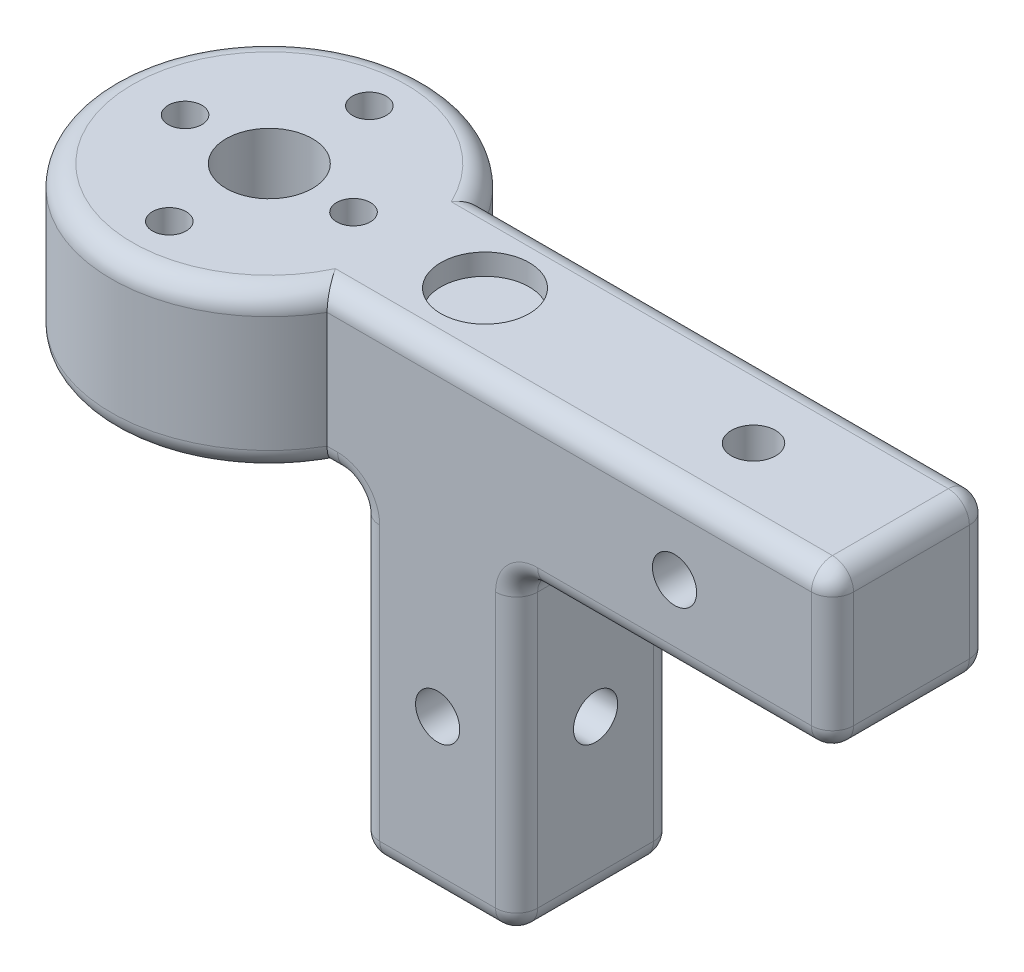
SolidWorks part; units mm, degrees
ref_plane "Front Plane" through (0, 0, 0) normal (0, 0, 1) x (1, 0, 0)
ref_plane "Top Plane" through (0, 0, 0) normal (0, 1, 0) x (1, 0, 0)
ref_plane "Right Plane" through (0, 0, 0) normal (1, 0, 0) x (0, 0, -1)
sketch "Sketch1" plane through (0, 0, 0) normal (0, 1, 0) x (1, 0, 0)
  line L0 (0, 0) -> (60.9904, 0) construction
  line L1 (12.9904, 7.5) -> (60.9904, 7.5)
  line L2 (15.9904, 7.5) -> (15.9904, -7.5) construction
  line L3 (12.9904, -7.5) -> (60.9904, -7.5)
  line L4 (60.9904, 7.5) -> (60.9904, -7.5)
  line L5 (12.9904, 7.5) -> (12.9904, -7.5) construction
  arc A0 (12.9904, 7.5) -> (12.9904, -7.5) centre (0, 0) ccw
  dimension "D1" = 30
  dimension "D2" = 15
  dimension "D3" = 45
  dimension "D4" = 3
extrude "Boss-Extrude1" add sketch "Sketch1" along normal blind 15
sketch "Sketch2" plane through (0, 15, 0) normal (0, 1, 0) x (1, 0, 0)
  line L0 (60.9904, -7.5) -> (60.9904, 7.5) construction
  circle A0 centre (0, 0) radius 4.1
  circle A1 centre (0, 9.5) radius 1.6
  circle A2 centre (0, -9.5) radius 1.6
  circle A3 centre (-8, 0) radius 1.6
  circle A4 centre (8, 0) radius 1.6
  circle A6 centre (45.9904, 0) radius 2.1
  point P15 (60.9904, 0)
  dimension "D1" = 8.2
  dimension "D2" = 3.2
  dimension "D3" = 3.2
  dimension "D4" = 3.2
  dimension "D5" = 3.2
  dimension "D10" = 15
  dimension "D13" = 4.2
  dimension "D6" = 8
  dimension "D7" = 8
  dimension "D8" = 9.5
  dimension "D9" = 9.5
extrude "top-gaten" cut sketch "Sketch2" against normal blind 15
sketch "Sketch3" plane through (0, 0, 0) normal (0, -1, 0) x (1, 0, 0)
  line L1 (15.9904, 7.5) -> (30.9904, 7.5)
  line L2 (15.9904, 7.5) -> (15.9904, -7.5)
  line L3 (15.9904, -7.5) -> (30.9904, -7.5)
  line L4 (30.9904, 7.5) -> (30.9904, -7.5)
  dimension "D1" = 15
  dimension "D2" = 3
extrude "Onder-extrude" add sketch "Sketch3" along normal blind 30
sketch "Sketch4" plane through (0, 0, 7.5) normal (0, 0, 1) x (1, 0, 0)
  line L0 (15.9904, -30) -> (15.9904, 0) construction
  line L1 (30.9904, -30) -> (15.9904, -30) construction
  line L2 (30.9904, 0) -> (60.9904, 0) construction
  line L3 (60.9904, 15) -> (60.9904, 0) construction
  circle A1 centre (45.9904, 7.5) radius 2.1
  circle A3 centre (23.4904, -15) radius 2.1
  dimension "D1" = 4.2
  dimension "D4" = 4.2
  dimension "D5" = 7.5
  dimension "D6" = 15
  dimension "D8" = 7.5
  dimension "D9" = 15
extrude "Z-gaten" cut sketch "Sketch4" against normal blind 15
sketch "Sketch5" plane through (30.9904, 0, 0) normal (1, 0, 0) x (0, 0, -1)
  line L0 (7.5, -30) -> (-7.5, -30) construction
  line L1 (-7.5, -30) -> (-7.5, 0) construction
  circle A1 centre (0, -15) radius 2.1
  dimension "D1" = 4.2
  dimension "D3" = 15
  dimension "D5" = 7.5
extrude "Cut-Extrude3" cut sketch "Sketch5" against normal blind 15
sketch "Sketch6" plane through (0, 15, 0) normal (0, 1, 0) x (1, 0, 0)
  line L3 (60.9904, -7.5) -> (60.9904, 7.5) construction
  line L4 (12.9904, -7.5) -> (60.9904, -7.5) construction
  circle A0 centre (20.4904, 0) radius 4.2
  dimension "D1" = 40.5
  dimension "D3" = 8.4
  dimension "D2" = 7.5
extrude "Cut-Extrude4" cut sketch "Sketch6" against normal blind 2
fillet "Fillet2" radius 2 23 edges at (-15, 15, 0) (0, 0, 4.1) (-15, 0, 0) (60.9904, 7.5, -7.5) (60.9904, 15, 0) (36.9904, 15, -7.5) (30.9904, -30, 0) (23.4904, -30, -7.5) (15.9904, -30, 0) (23.4904, -30, 7.5) (60.9904, 0, 0) (36.9904, 15, 7.5) (60.9904, 7.5, 7.5)
